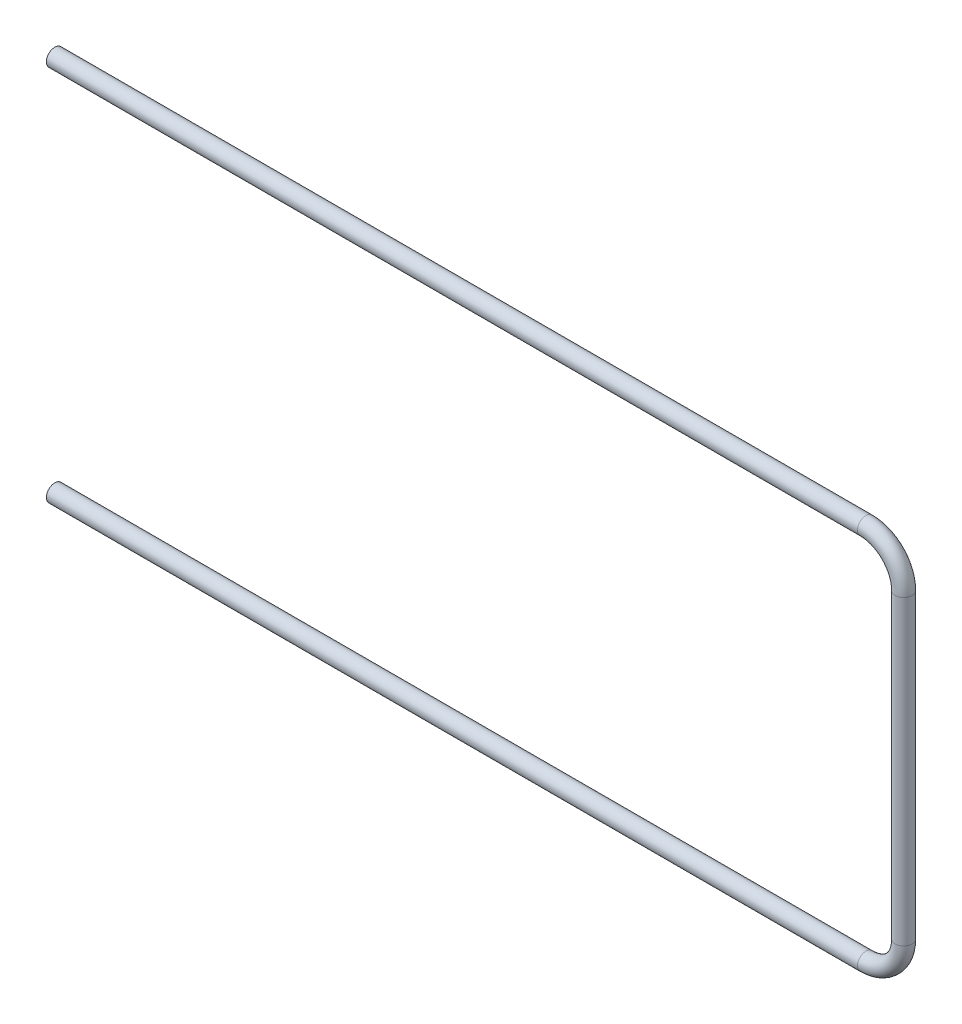
SolidWorks part; units mm, degrees
ref_plane "Front Plane" through (0, 0, 0) normal (0, 0, 1) x (1, 0, 0)
ref_plane "Top Plane" through (0, 0, 0) normal (0, 1, 0) x (1, 0, 0)
ref_plane "Right Plane" through (0, 0, 0) normal (1, 0, 0) x (0, 0, -1)
sketch "Sketch1" plane through (0, 0, 0) normal (1, 0, 0) x (0, 0, -1)
  circle A0 centre (0, 0) radius 2.5
  circle A1 centre (0, 0) radius 4.5
  dimension "D1" = 5
sketch "Sketch2" plane through (0, 0, 0) normal (0, 0, 1) x (1, 0, 0)
  line L0 (0, 0) -> (430, 0)
  line L1 (450, -20) -> (450, -180)
  line L2 (430, -200) -> (0, -200)
  arc A0 (450, -180) -> (430, -200) centre (430, -180) cw
  arc A1 (430, 0) -> (450, -20) centre (430, -20) cw
  point P7 (450, -200)
  point P10 (450, 0)
  dimension "D3" = 20
  dimension "D1" = 450
  dimension "D2" = 200
sweep "Sweep1" add profiles "Sketch1" path "Sketch2"
